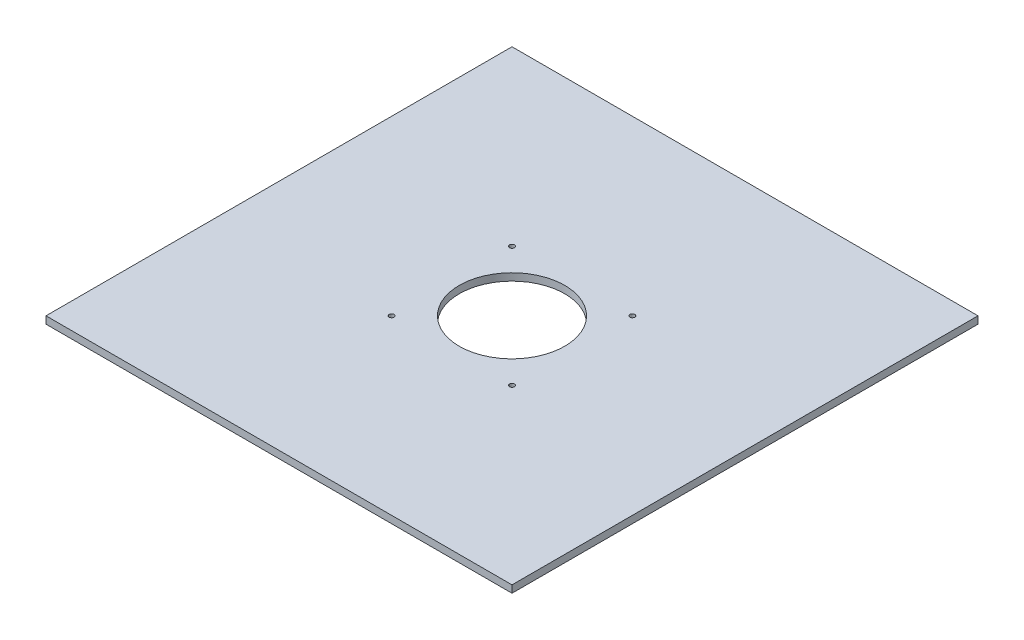
SolidWorks part; units mm, degrees
material "Oak"
ref_plane "Front" through (0, 0, 0) normal (0, 0, 1) x (1, 0, 0)
ref_plane "Top" through (0, 0, 0) normal (0, 1, 0) x (1, 0, 0)
ref_plane "Right" through (0, 0, 0) normal (1, 0, 0) x (0, 0, -1)
sketch "Sketch1" plane through (0, 0, 0) normal (0, 1, 0) x (1, 0, 0)
  line L1 (-203.2, 203.2) -> (203.2, 203.2)
  line L2 (-203.2, 203.2) -> (-203.2, -203.2)
  line L3 (-203.2, -203.2) -> (203.2, -203.2)
  line L4 (203.2, 203.2) -> (203.2, -203.2)
  point P4 (0, 203.2)
  point P6 (203.2, 0)
  dimension "D1" = 406.4
  dimension "D2" = 406.4
extrude "Boss-Extrude1" add sketch "Sketch1" along normal blind 6.35
sketch "Sketch2" plane through (0, 6.35, 0) normal (0, 1, 0) x (1, 0, 0)
  circle A0 centre (0, 0) radius 46
  circle A1 centre (52.5, 52.5) radius 2.15
  circle A2 centre (52.5, -52.5) radius 2.15
  circle A3 centre (-52.5, -52.5) radius 2.15
  circle A4 centre (-52.5, 52.5) radius 2.165
  point P11 (0, 0)
  point P12 (0, 0)
  point P13 (0, 0)
  point P14 (0, 0)
  dimension "D1" = 92
  dimension "D2" = 4.33
  dimension "D3" = 4.3
  dimension "D4" = 4.3
  dimension "D5" = 4.3
  dimension "D6" = 52.5
  dimension "D7" = 52.5
  dimension "D8" = 52.5
  dimension "D9" = 52.5
extrude "Cut-Extrude1" cut sketch "Sketch2" against normal up to next
